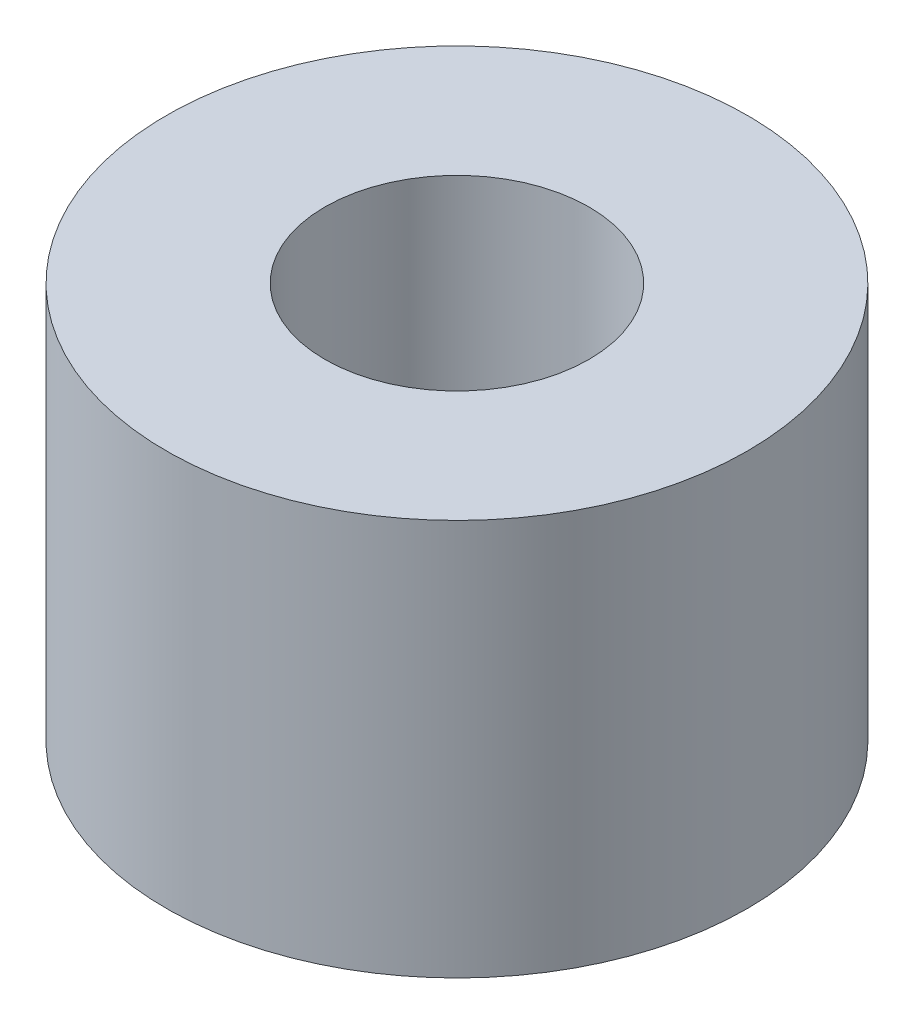
SolidWorks part; units mm, degrees
material "ABS"
ref_plane "Front Plane" through (0, 0, 0) normal (0, 0, 1) x (1, 0, 0)
ref_plane "Top Plane" through (0, 0, 0) normal (0, 1, 0) x (1, 0, 0)
ref_plane "Right Plane" through (0, 0, 0) normal (1, 0, 0) x (0, 0, -1)
sketch "Sketch1" plane through (0, 0, 0) normal (0, 0, 1) x (1, 0, 0)
  line L1 (0, -1.5) -> (0, 1.5)
  line L2 (-2.2, 1.5) -> (0, 1.5)
  line L3 (-2.2, 1.5) -> (-2.2, -1.5)
  line L4 (-2.2, -1.5) -> (0, -1.5)
  point P1 (0, 0)
  dimension "D1" = 2.2
  dimension "D3" = 3
revolve "main body " add sketch "Sketch1" angle 360 about L1
sketch "Sketch2" plane through (0, 1.5, 0) normal (0, 1, 0) x (1, 0, 0)
  circle A0 centre (0, 0) radius 1
  dimension "D1" = 2
extrude "tendon hole " cut sketch "Sketch2" against normal up to surface (3 mm away) contours A0 up to face at (2.2, -1.5, 0)
